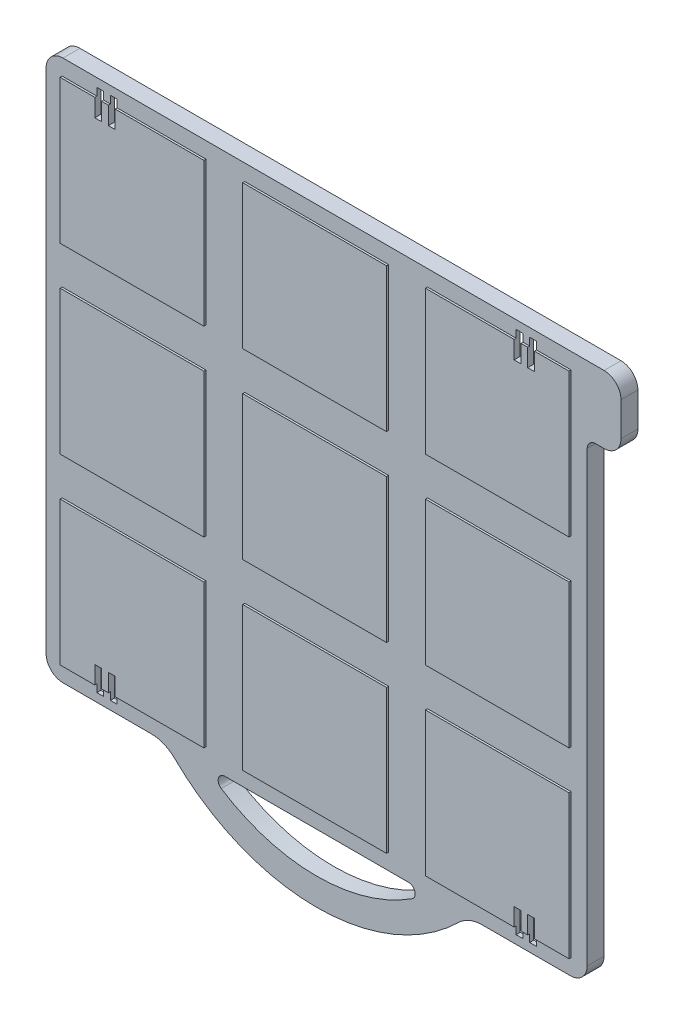
SolidWorks part; units mm, degrees
ref_plane "Front Plane" through (0, 0, 0) normal (0, 0, 1) x (1, 0, 0)
ref_plane "Top Plane" through (0, 0, 0) normal (0, 1, 0) x (1, 0, 0)
ref_plane "Right Plane" through (0, 0, 0) normal (1, 0, 0) x (0, 0, -1)
sketch "Sketch1" plane through (0, 0, 0) normal (0, 0, 1) x (1, 0, 0)
  line L0 (101.6, 101.6) -> (107.95, 101.6)
  line L1 (-95.25, 101.6) -> (101.6, 101.6)
  line L2 (-101.6, 95.25) -> (-101.6, -95.25)
  line L3 (-95.25, -101.6) -> (-62.217, -101.6)
  line L4 (101.6, 73.025) -> (101.6, -95.25)
  line L5 (-101.6, 101.6) -> (101.6, -101.6) construction
  line L6 (-101.6, -101.6) -> (101.6, 101.6) construction
  line L7 (114.3, 95.25) -> (114.3, 82.55)
  line L8 (107.95, 76.2) -> (104.775, 76.2)
  line L9 (0, -50.8) -> (0, 0) construction
  line L10 (-34.4542, -101.6) -> (34.4542, -101.6)
  line L11 (62.217, -101.6) -> (95.25, -101.6)
  arc A0 (53.3289, -105.2286) -> (-53.3289, -105.2286) centre (0, -50.8) cw
  arc A1 (-35.8324, -106.2736) -> (35.8324, -106.2736) centre (0, -50.8) ccw
  arc A2 (53.3289, -105.2286) -> (62.217, -101.6) centre (62.217, -114.3) cw
  arc A3 (-53.3289, -105.2286) -> (-62.217, -101.6) centre (-62.217, -114.3) ccw
  arc A4 (35.8324, -106.2736) -> (34.4542, -101.6) centre (34.4542, -104.14) ccw
  arc A5 (-35.8324, -106.2736) -> (-34.4542, -101.6) centre (-34.4542, -104.14) cw
  arc A6 (114.3, 82.55) -> (107.95, 76.2) centre (107.95, 82.55) cw
  arc A7 (-101.6, -95.25) -> (-95.25, -101.6) centre (-95.25, -95.25) ccw
  arc A8 (95.25, -101.6) -> (101.6, -95.25) centre (95.25, -95.25) ccw
  arc A9 (107.95, 101.6) -> (114.3, 95.25) centre (107.95, 95.25) cw
  arc A10 (-95.25, 101.6) -> (-101.6, 95.25) centre (-95.25, 95.25) ccw
  arc A11 (104.775, 76.2) -> (101.6, 73.025) centre (104.775, 73.025) ccw
  point P0 (0, 0)
  point P18 (56.7961, -101.6)
  point P23 (42.1976, -101.6)
  point P26 (-42.1976, -101.6)
  dimension "D3" = 76.2
  dimension "D5" = 66.04
  dimension "D6" = 12.7
  dimension "D7" = 2.54
  dimension "D8" = 6.35
  dimension "D11" = 3.175
  dimension "D1" = 203.2
  dimension "D2" = 203.2
  dimension "D4" = 50.8
  dimension "D9" = 12.7
  dimension "D10" = 25.4
  dimension "D12" = 203.2
extrude "Boss-Extrude1" add sketch "Sketch1" along normal blind 6.35
shell "Shell1" thickness 1.524
sketch "Sketch2" plane through (0, 0, 6.35) normal (0, 0, 1) x (1, 0, 0)
  line L0 (41.5925, 26.9875) -> (41.5925, -26.9875)
  line L1 (-26.9875, 26.9875) -> (26.9875, 26.9875)
  line L2 (-26.9875, 26.9875) -> (-26.9875, -26.9875)
  line L3 (-26.9875, -26.9875) -> (26.9875, -26.9875)
  line L4 (26.9875, 26.9875) -> (26.9875, -26.9875)
  line L5 (-26.9875, 26.9875) -> (26.9875, -26.9875) construction
  line L6 (-26.9875, -26.9875) -> (26.9875, 26.9875) construction
  line L7 (41.5925, 26.9875) -> (95.5675, 26.9875)
  line L8 (95.5675, 26.9875) -> (95.5675, -26.9875)
  line L9 (41.5925, -26.9875) -> (95.5675, -26.9875)
  line L10 (41.5925, 95.5675) -> (41.5925, 41.5925)
  line L11 (41.5925, 41.5925) -> (95.5675, 41.5925)
  line L12 (95.5675, 95.5675) -> (95.5675, 41.5925)
  line L13 (41.5925, 95.5675) -> (95.5675, 95.5675)
  line L14 (95.5675, -41.5925) -> (41.5925, -41.5925)
  line L15 (41.5925, -41.5925) -> (41.5925, -95.5675)
  line L16 (95.5675, -95.5675) -> (41.5925, -95.5675)
  line L17 (95.5675, -41.5925) -> (95.5675, -95.5675)
  line L18 (26.9875, -41.5925) -> (-26.9875, -41.5925)
  line L19 (-26.9875, -41.5925) -> (-26.9875, -95.5675)
  line L20 (26.9875, -95.5675) -> (-26.9875, -95.5675)
  line L21 (26.9875, -41.5925) -> (26.9875, -95.5675)
  line L22 (-41.5925, -95.5675) -> (-41.5925, -41.5925)
  line L23 (-41.5925, -41.5925) -> (-95.5675, -41.5925)
  line L24 (-95.5675, -95.5675) -> (-95.5675, -41.5925)
  line L25 (-41.5925, -95.5675) -> (-95.5675, -95.5675)
  line L26 (-41.5925, -26.9875) -> (-41.5925, 26.9875)
  line L27 (-41.5925, 26.9875) -> (-95.5675, 26.9875)
  line L28 (-95.5675, -26.9875) -> (-95.5675, 26.9875)
  line L29 (-41.5925, -26.9875) -> (-95.5675, -26.9875)
  line L30 (-95.5675, 41.5925) -> (-41.5925, 41.5925)
  line L31 (-41.5925, 41.5925) -> (-41.5925, 95.5675)
  line L32 (-95.5675, 95.5675) -> (-41.5925, 95.5675)
  line L33 (-95.5675, 41.5925) -> (-95.5675, 95.5675)
  line L34 (-26.9875, 41.5925) -> (26.9875, 41.5925)
  line L35 (26.9875, 41.5925) -> (26.9875, 95.5675)
  line L36 (-26.9875, 95.5675) -> (26.9875, 95.5675)
  line L37 (-26.9875, 41.5925) -> (-26.9875, 95.5675)
  point P0 (0, 0)
  point P41 (0, 0)
  dimension "D1" = 53.975
  dimension "D2" = 53.975
  dimension "D4" = 68.58
  dimension "D6" = 68.58
  dimension "D8" = 68.58
  dimension "D9" = 68.58
  dimension "D3" = 2
  dimension "D5" = 2
  dimension "D7" = 4
extrude "Boss-Extrude2" add sketch "Sketch2" along normal blind 0.762
sketch "Sketch3" plane through (0, 0, 7.112) normal (0, 0, 1) x (1, 0, 0)
  line L0 (0, 162.3035) -> (0, 0) construction
  line L1 (0, 0) -> (217.1484, 0) construction
  line L2 (107.95, 101.6) -> (-95.25, 101.6) construction
  line L3 (-82.55, 98.425) -> (-80.01, 98.425)
  line L4 (-82.55, 98.425) -> (-82.55, 88.9)
  line L5 (-82.55, 88.9) -> (-80.01, 88.9)
  line L6 (-80.01, 98.425) -> (-80.01, 88.9)
  line L7 (-77.47, 98.425) -> (-74.93, 98.425)
  line L8 (-77.47, 98.425) -> (-77.47, 88.9)
  line L9 (-77.47, 88.9) -> (-74.93, 88.9)
  line L10 (-74.93, 98.425) -> (-74.93, 88.9)
  line L11 (-101.6, 95.25) -> (-101.6, -95.25) construction
  line L12 (74.93, 98.425) -> (74.93, 88.9)
  line L13 (77.47, 88.9) -> (74.93, 88.9)
  line L14 (77.47, 98.425) -> (77.47, 88.9)
  line L15 (77.47, 98.425) -> (74.93, 98.425)
  line L16 (80.01, 98.425) -> (80.01, 88.9)
  line L17 (82.55, 88.9) -> (80.01, 88.9)
  line L18 (82.55, 98.425) -> (82.55, 88.9)
  line L19 (82.55, 98.425) -> (80.01, 98.425)
  line L20 (82.55, -98.425) -> (80.01, -98.425)
  line L21 (82.55, -98.425) -> (82.55, -88.9)
  line L22 (82.55, -88.9) -> (80.01, -88.9)
  line L23 (80.01, -98.425) -> (80.01, -88.9)
  line L24 (77.47, -98.425) -> (74.93, -98.425)
  line L25 (77.47, -98.425) -> (77.47, -88.9)
  line L26 (77.47, -88.9) -> (74.93, -88.9)
  line L27 (74.93, -98.425) -> (74.93, -88.9)
  line L28 (-74.93, -98.425) -> (-74.93, -88.9)
  line L29 (-77.47, -88.9) -> (-74.93, -88.9)
  line L30 (-77.47, -98.425) -> (-77.47, -88.9)
  line L31 (-77.47, -98.425) -> (-74.93, -98.425)
  line L32 (-80.01, -98.425) -> (-80.01, -88.9)
  line L33 (-82.55, -88.9) -> (-80.01, -88.9)
  line L34 (-82.55, -98.425) -> (-82.55, -88.9)
  line L35 (-82.55, -98.425) -> (-80.01, -98.425)
  point P16 (-74.93, 93.6625)
  dimension "D1" = 2.54
  dimension "D2" = 9.525
  dimension "D3" = 3.175
  dimension "D4" = 19.05
  dimension "D5" = 5.08
extrude "Cut-Extrude1" cut sketch "Sketch3" against normal through all
sketch "Sketch4" plane through (0, 0, 4.826) normal (0, 0, -1) x (-1, 0, 0)
  circle A0 centre (0, 0) radius 4.7625
  circle A1 centre (0, 0) radius 6.2865
  dimension "D1" = 9.525
  dimension "D2" = 12.573
extrude "Boss-Extrude3" add sketch "Sketch4" along normal up to surface (4.826 mm away) up to face at (0, -106.3208, 0)
sketch "Sketch5" plane through (0, 0, 0) normal (0, 0, -1) x (-1, 0, 0)
  line L0 (6.2865, 0) -> (100.076, 0)
  line L1 (100.076, 95.25) -> (100.076, -95.25) construction
  line L2 (-6.2865, 0) -> (-100.076, 0)
  line L3 (-100.076, -95.25) -> (-100.076, 73.025) construction
  line L4 (0, -6.2865) -> (0, -100.076)
  line L5 (-34.4542, -100.076) -> (34.4542, -100.076) construction
  line L6 (0, 6.2865) -> (0, 100.076)
  line L7 (-107.95, 100.076) -> (95.25, 100.076) construction
  line L8 (4.4452, 4.4452) -> (98.6625, 98.6625)
  line L9 (4.4452, -4.4452) -> (98.6625, -98.6625)
  line L10 (-4.4452, -4.4452) -> (-98.6625, -98.6625)
  line L11 (-4.4452, 4.4452) -> (-100.076, 100.076)
  line L13 (-107.95, 100.076) -> (95.25, 100.076) construction
  circle A0 centre (0, 0) radius 6.2865 construction
  circle A1 centre (0, 0) radius 6.2865 construction
  arc A5 (100.076, 95.25) -> (95.25, 100.076) centre (95.25, 95.25) ccw construction
  arc A6 (95.25, -100.076) -> (100.076, -95.25) centre (95.25, -95.25) ccw construction
  arc A7 (-100.076, -95.25) -> (-95.25, -100.076) centre (-95.25, -95.25) ccw construction
  dimension "D1" = 45
  dimension "D2" = 45
rib "Rib1" sketch "Sketch5" sketch "Sketch5" thickness 1.27 extrusion direction normal to sketch draft on no parameters "D1"=1.27
